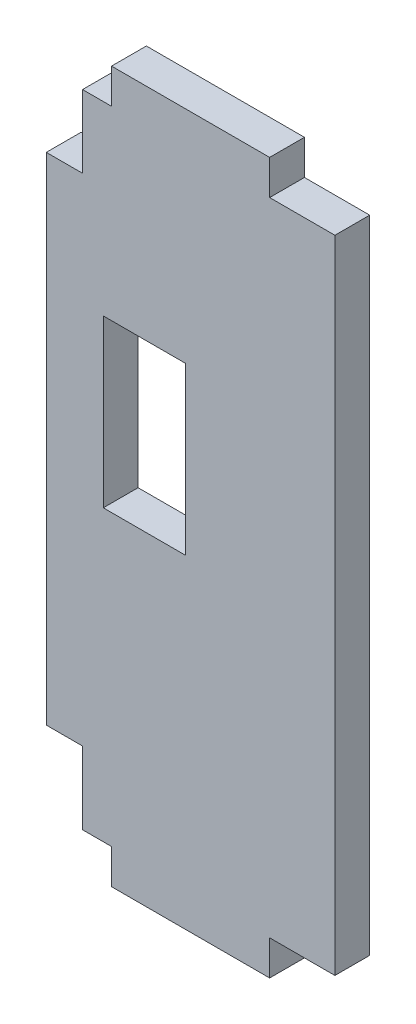
SolidWorks part; units mm, degrees
ref_plane "Front Plane" through (0, 0, 0) normal (0, 0, 1) x (1, 0, 0)
ref_plane "Top Plane" through (0, 0, 0) normal (0, 1, 0) x (1, 0, 0)
ref_plane "Right Plane" through (0, 0, 0) normal (1, 0, 0) x (0, 0, -1)
sketch "Sketch1" plane through (0, 0, 0) normal (0, 0, 1) x (1, 0, 0)
  line L1 (-15.5321, -16.8148) -> (-8.3439, -16.8148)
  line L2 (-15.5321, -16.8148) -> (-15.5321, -31.369)
  line L3 (-15.5321, -31.369) -> (-8.3439, -31.369)
  line L4 (-8.3439, -16.8148) -> (-8.3439, -31.369)
  line L6 (-17.3482, -0.5588) -> (-17.3482, -6.9088)
  line L7 (-17.3482, -6.9088) -> (-20.5232, -6.9088)
  line L8 (-20.5232, -6.9088) -> (-20.5232, -50.3428)
  line L9 (-20.5232, -50.3428) -> (-17.3482, -50.3428)
  line L10 (-17.3482, -50.3428) -> (-17.3482, -56.6928)
  line L11 (-17.3482, -0.5588) -> (-14.8082, -0.5588)
  line L12 (-14.8082, -0.5588) -> (-14.8082, 2.4892)
  line L13 (-14.8082, 2.4892) -> (-0.9652, 2.4892)
  line L14 (-0.9652, 2.4892) -> (-0.9652, -0.5588)
  line L15 (-0.9652, -0.5588) -> (4.7498, -0.5588)
  line L16 (4.7498, -0.5588) -> (4.7498, -56.6928)
  line L18 (4.7498, -56.6928) -> (-0.9652, -56.6928)
  line L19 (-0.9652, -56.6928) -> (-0.9652, -59.7408)
  line L20 (-0.9652, -59.7408) -> (-14.8082, -59.7408)
  line L21 (-14.8082, -59.7408) -> (-14.8082, -56.6928)
  line L22 (-14.8082, -56.6928) -> (-17.3482, -56.6928)
  line L23 (-20.5232, -0.5588) -> (-20.5232, -6.9088) construction
  line L27 (-0.9652, -56.6928) -> (-14.8082, -56.6928) construction
  line L28 (-0.9652, -59.7408) -> (-14.8082, -59.7408) construction
  dimension "D1" = 19.304
  dimension "D2" = 7.1882
  dimension "D3" = 14.5542
  dimension "D4" = 9.0043
  dimension "D6" = 3.048
  dimension "D8" = 6.35
extrude "Boss-Extrude1" add sketch "Sketch1" along normal blind 3.048
